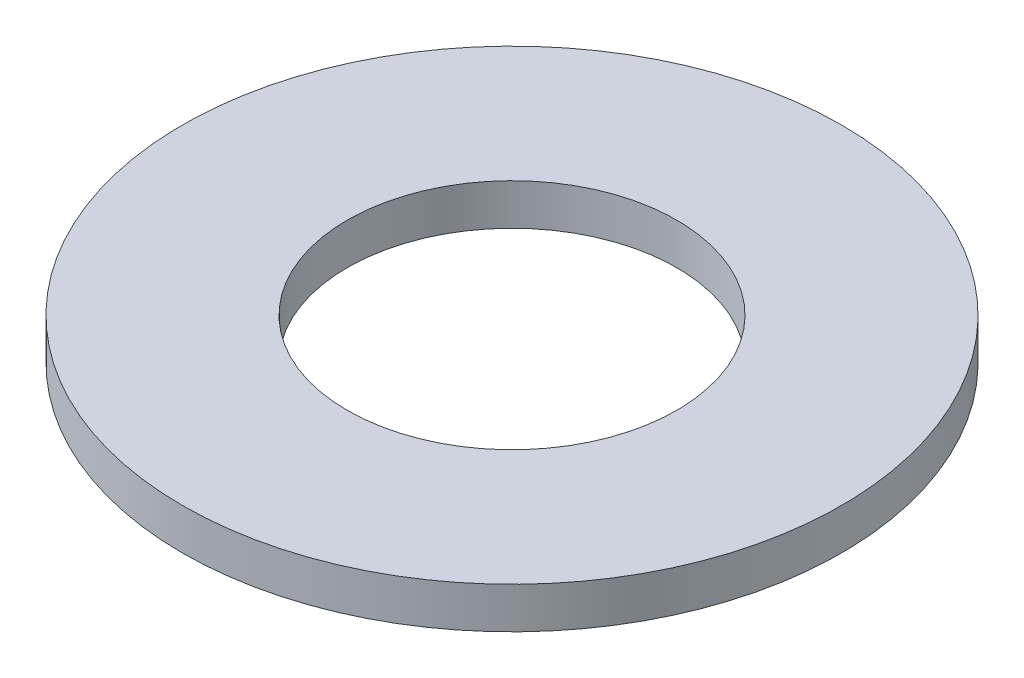
SolidWorks part; units mm, degrees
ref_plane "Front Plane" through (0, 0, 0) normal (0, 0, 1) x (1, 0, 0)
ref_plane "Top Plane" through (0, 0, 0) normal (0, 1, 0) x (1, 0, 0)
ref_plane "Right Plane" through (0, 0, 0) normal (1, 0, 0) x (0, 0, -1)
sketch "Sketch1" plane through (0, 0, 0) normal (0, 1, 0) x (1, 0, 0)
  circle A0 centre (0, 0) radius 12.7
  circle A1 centre (0, 0) radius 25.4
  dimension "D1" = 50.8
  dimension "D2" = 25.4
extrude "Boss-Extrude1" add sketch "Sketch1" along normal blind 3.175
